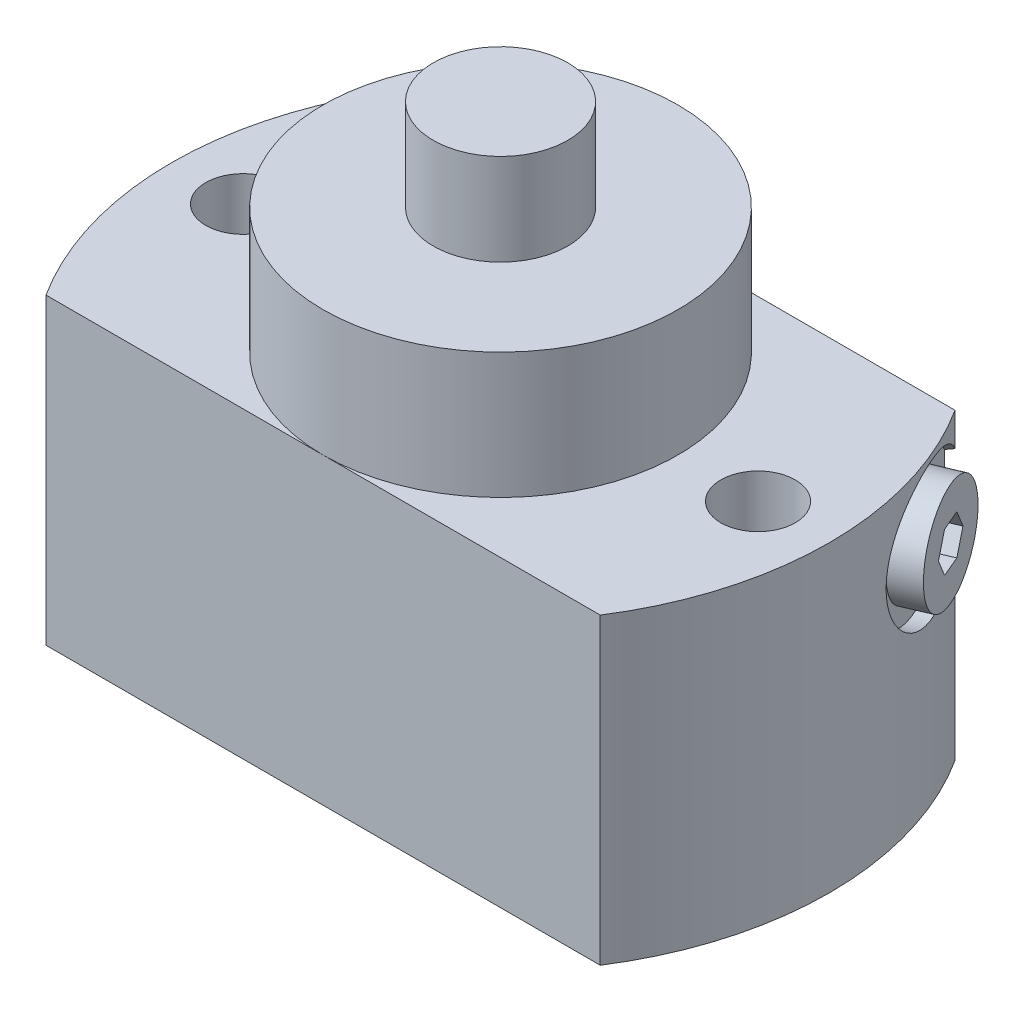
SolidWorks part; units mm, degrees
material "Alloy Steel"
ref_plane "Front Plane" through (0, 0, 0) normal (0, 0, 1) x (1, 0, 0)
ref_plane "Top Plane" through (0, 0, 0) normal (0, 1, 0) x (1, 0, 0)
ref_plane "Right Plane" through (0, 0, 0) normal (1, 0, 0) x (0, 0, -1)
sketch "Sketch1" plane through (0, 0, 0) normal (0, 1, 0) x (1, 0, 0)
  line L0 (-48.4278, 31) -> (48.4278, 31)
  line L1 (0, 0) -> (70.7148, 0) construction
  line L2 (-48.4278, -31) -> (48.4278, -31)
  arc A0 (-48.4278, 31) -> (-48.4278, -31) centre (0, 0) ccw
  arc A1 (48.4278, -31) -> (48.4278, 31) centre (0, 0) ccw
  dimension "D1" = 57.5
  dimension "D2" = 62
extrude "Extrude1" add sketch "Sketch1" along normal blind 53
sketch "Sketch2" plane through (0, 0, 0) normal (0, 0, 1) x (1, 0, 0)
  line L0 (0, 0) -> (0, 90.1953) construction
  line L1 (0, 91) -> (-11.75, 91)
  line L2 (-11.75, 91) -> (-11.75, 75)
  line L3 (-11.75, 75) -> (-31, 75)
  line L6 (-31, 75) -> (-31, 53)
  line L7 (-48.4278, 53) -> (48.4278, 53) construction
  line L8 (-31, 53) -> (0, 53)
  line L9 (0, 53) -> (0, 91)
  line L10 (-48.4278, 0) -> (48.4278, 0) construction
  point P8 (-33.2109, 75)
  dimension "D1" = 23.5
  dimension "D2" = 16
  dimension "D3" = 75
  dimension "D6" = 62
revolve "Revolve1" add sketch "Sketch2" angle 360 about L0
hole_wizard "Hole1" positions "Sketch4" profile "Sketch3" legacy end condition up to next
sketch "Sketch4" plane through (0, 53, 0) normal (0, 1, 0) x (-1, 0, 0)
  line L0 (0, 0) -> (0, 47.5777) construction
  point P0 (45, 0)
  point P7 (-45, 0)
  dimension "D1" = 90
sketch "Sketch3" plane through (-45, 53, 0) normal (1, 0, 0) x (0, 0, 1)
  line L0 (0, 0) -> (0, 53)
  line L1 (0, 53) -> (6.5, 53)
  line L2 (6.5, 53) -> (6.5, 0)
  line L3 (6.5, 0) -> (0, 0)
  line L4 (0, 110) -> (0, -10) construction
  dimension "Diameter" = 13
  dimension "Depth" = 53
sketch "Sketch5" plane through (0, 0, 0) normal (0, -1, 0) x (1, 0, 0)
  circle A0 centre (0, 0) radius 4
  dimension "D1" = 8
extrude "Cut-Extrude1" cut sketch "Sketch5" against normal blind 4
sketch "Sketch6" plane through (0, 0, 0) normal (0, -1, 0) x (1, 0, 0)
  circle A0 centre (35, -15) radius 5.5
  dimension "D3" = 11
  dimension "D1" = 35
  dimension "D2" = 15
extrude "Cut-Extrude2" cut sketch "Sketch6" against normal blind 3
sketch "Sketch7" plane through (0, 3, 0) normal (0, -1, 0) x (1, 0, 0)
  circle A0 centre (35, -15) radius 2
  dimension "D1" = 4
extrude "Cut-Extrude3" cut sketch "Sketch7" against normal blind 33
ref_plane "Plane1" through (0, 0, 0) normal (0.3907, 0, 0.9205) x (0.9205, 0, -0.3907)
sketch "Sketch8" plane through (0, 0, 0) normal (0.3907, 0, 0.9205) x (0.9205, 0, -0.3907)
  line L0 (51.5856, 40) -> (-19.0781, 40) construction
  line L1 (-56.6907, 0) -> (32.4653, 0) construction
  line L2 (57.5, 28) -> (55, 28)
  line L3 (57.5, 0) -> (57.5, 53) construction
  line L4 (55, 28) -> (55, 33.4215)
  line L5 (55, 33.4215) -> (53.5174, 34.2775)
  line L6 (53.5174, 34.2775) -> (35, 34.2775)
  line L7 (35, 34.2775) -> (35, 40)
  line L8 (35, 40) -> (57.5, 40)
  line L9 (57.5, 40) -> (57.5, 28)
  dimension "D1" = 40
  dimension "D2" = 2.5
  dimension "D3" = 20
  dimension "D4" = 11.445
  dimension "D5" = 24
  dimension "D6" = 30
  dimension "D7" = 13.157
revolve "Cut-Revolve1" cut sketch "Sketch8" angle 360 about L0
sketch "Sketch9" plane through (0, 0, 0) normal (0.3907, 0, 0.9205) x (0.9205, 0, -0.3907)
  line L0 (74.5879, 40) -> (15.4121, 40) construction
  line L1 (35, 40) -> (53.5174, 40) construction
  line L2 (55, 28) -> (55, 52) construction
  line L4 (55, 31) -> (55, 34.2775)
  line L5 (46, 34.2775) -> (55, 34.2775)
  line L6 (55, 31) -> (60, 31)
  line L7 (60, 31) -> (60, 40)
  line L8 (60, 40) -> (45, 40)
  line L9 (45, 40) -> (45, 35.2775)
  line L10 (45, 35.2775) -> (46, 34.2775)
  line L12 (40.0743, 34.2775) -> (53.5174, 34.2775) construction
  dimension "D1" = 45
  dimension "D2" = 4.7225
  dimension "D3" = 10
  dimension "D4" = 5
  dimension "D5" = 18
revolve "Revolve2" add sketch "Sketch9" angle 360 about L0
sketch "Sketch10" plane through (55.2303, 0, -23.4439) normal (0.9205, 0, -0.3907) x (-0.3907, 0, -0.9205)
  line L1 (4.0415, 40) -> (2.0207, 43.5)
  line L2 (2.0207, 43.5) -> (-2.0207, 43.5)
  line L3 (-2.0207, 43.5) -> (-4.0415, 40)
  line L4 (-4.0415, 40) -> (-2.0207, 36.5)
  line L5 (-2.0207, 36.5) -> (2.0207, 36.5)
  line L6 (2.0207, 36.5) -> (4.0415, 40)
  circle A0 centre (0, 40) radius 3.5 construction
  circle A1 centre (0, 40) radius 9 construction
  dimension "D1" = 7
extrude "Cut-Extrude4" cut sketch "Sketch10" against normal blind 5
